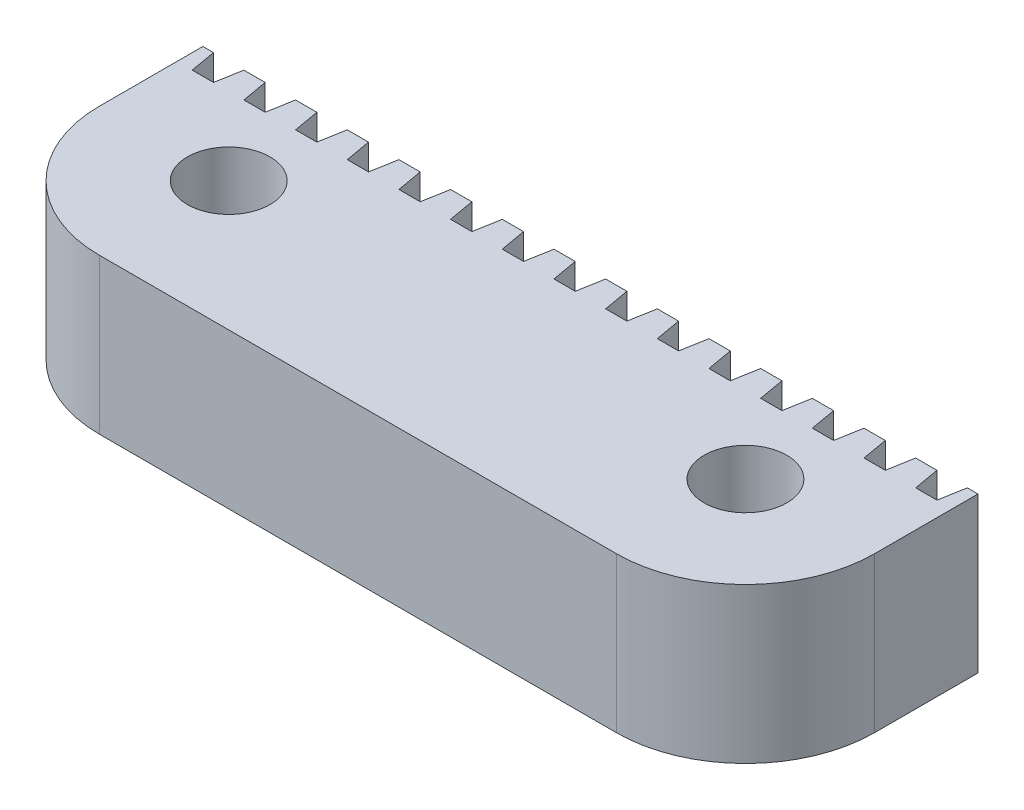
SolidWorks part; units mm, degrees
material "Maple"
ref_plane "Front Plane" through (0, 0, 0) normal (0, 0, 1) x (1, 0, 0)
ref_plane "Top Plane" through (0, 0, 0) normal (0, 1, 0) x (1, 0, 0)
ref_plane "Right Plane" through (0, 0, 0) normal (1, 0, 0) x (0, 0, -1)
sketch "Sketch1" plane through (0, 0, 0) normal (0, 1, 0) x (1, 0, 0)
  line L1 (0, 0) -> (30, 0)
  line L2 (0, 0) -> (0, 9)
  line L3 (0, 9) -> (30, 9)
  line L4 (30, 0) -> (30, 9)
  dimension "D1" = 30
  dimension "D2" = 9
extrude "Boss-Extrude1" add sketch "Sketch1" along normal blind 6
ref_plane "Plane1" through (0, 3, 0) normal (0, 1, 0) x (1, 0, 0)
ref_plane "Plane2" through (0, 0, -10) normal (0, 0, -1) x (-1, 0, 0)
sketch "Sketch2" plane through (0, 6, 0) normal (0, 1, 0) x (1, 0, 0)
  line L0 (15, 8) -> (15, 9) construction
  line L1 (14.4118, 9) -> (15.5882, 9)
  line L2 (14.4118, 9) -> (14.5882, 8)
  line L3 (14.5882, 8) -> (15.4118, 8)
  line L4 (15.4118, 8) -> (15.5882, 9)
  line L5 (14.5, 8.5) -> (15.5, 8.5) construction
  line L7 (30, 9) -> (0, 9) construction
  line L8 (0, 9) -> (0, 0) construction
  line L9 (30, 0) -> (30, 9) construction
  dimension "D1" = 10
  dimension "D2" = 1
  dimension "D3" = 1
extrude "Cut-Extrude1" cut sketch "Sketch2" against normal through all
pattern_linear "LPattern2" count 8 spacing 2 along (-1, 0, 0) count 8 spacing 2 along (1, 0, 0) of "Cut-Extrude1"
hole_wizard "M3 Clearance Hole1" positions "Sketch4" profile "Sketch3" hole size "M3" standard "ANSI Metric" end condition through all
sketch "Sketch4" plane through (0, 6, 0) normal (0, 1, 0) x (1, 0, 0)
  circle A0 centre (25, 5) radius 1.6 construction
  point P0 (5, 5)
  point P3 (25, 5)
sketch "Sketch3" plane through (5, 6, -5) normal (1, 0, 0) x (0, 0, 1)
  line L0 (0, 0) -> (0, 6)
  line L1 (0, 6) -> (1.6, 6)
  line L2 (1.6, 6) -> (1.6, 0)
  line L5 (1.6, 0) -> (0, 0)
  line L11 (0, -6.35) -> (0, 107.95) construction
  dimension "Thru Hole Dia." = 3.2
  dimension "Thru Hole Depth" = 6
fillet "Fillet1" radius 5 2 edges at (30, 3, 0) (0, 3, 0)
